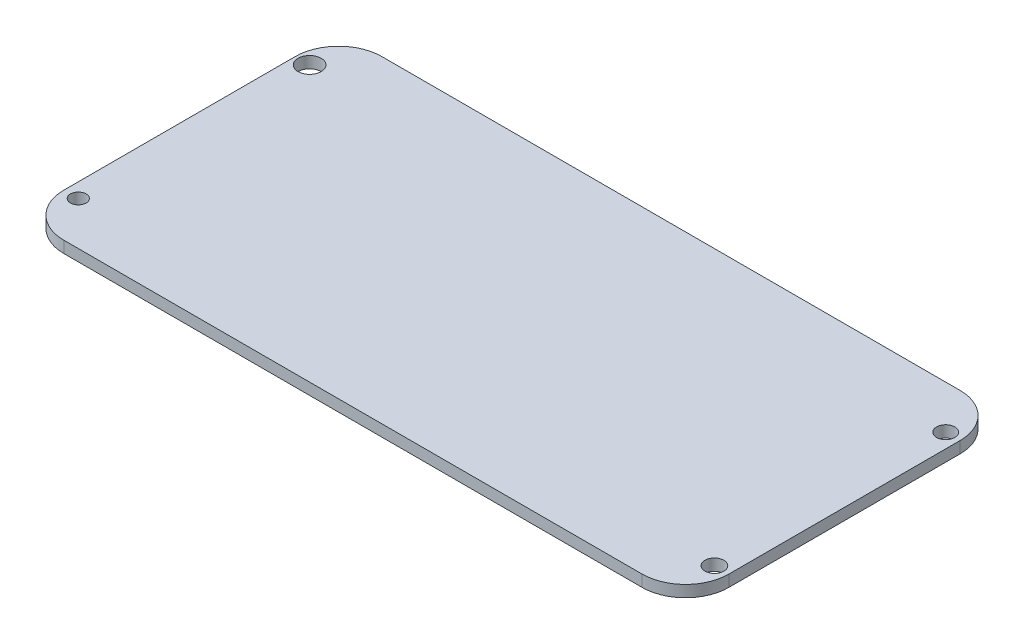
SolidWorks part; units mm, degrees
ref_plane "Front Plane" through (0, 0, 0) normal (0, 0, 1) x (1, 0, 0)
ref_plane "Top Plane" through (0, 0, 0) normal (0, 1, 0) x (1, 0, 0)
ref_plane "Right Plane" through (0, 0, 0) normal (1, 0, 0) x (0, 0, -1)
sketch "Sketch1" plane through (0, 0, 0) normal (0, 1, 0) x (1, 0, 0)
  line L1 (0, 0) -> (92, 0)
  line L2 (0, 0) -> (0, 44)
  line L3 (0, 44) -> (92, 44)
  line L4 (92, 0) -> (92, 44)
  circle A0 centre (2, 6) radius 1.0904
  circle A1 centre (2, 38) radius 1.6
  circle A2 centre (90, 38) radius 1.2645
  circle A3 centre (90, 6) radius 1.3087
  dimension "D3" = 3.2
  dimension "D1" = 92
  dimension "D2" = 44
  dimension "D4" = 6
  dimension "D5" = 2
  dimension "D6" = 6
  dimension "D7" = 2
  dimension "D8" = 6
  dimension "D9" = 2
  dimension "D10" = 2
  dimension "D11" = 6
extrude "Boss-Extrude1" add sketch "Sketch1" along normal blind 1.6
fillet "Fillet1" radius 6 4 edges at (0, 0.8, -44) (92, 0.8, -44) (92, 0.8, 0) (0, 0.8, 0)
